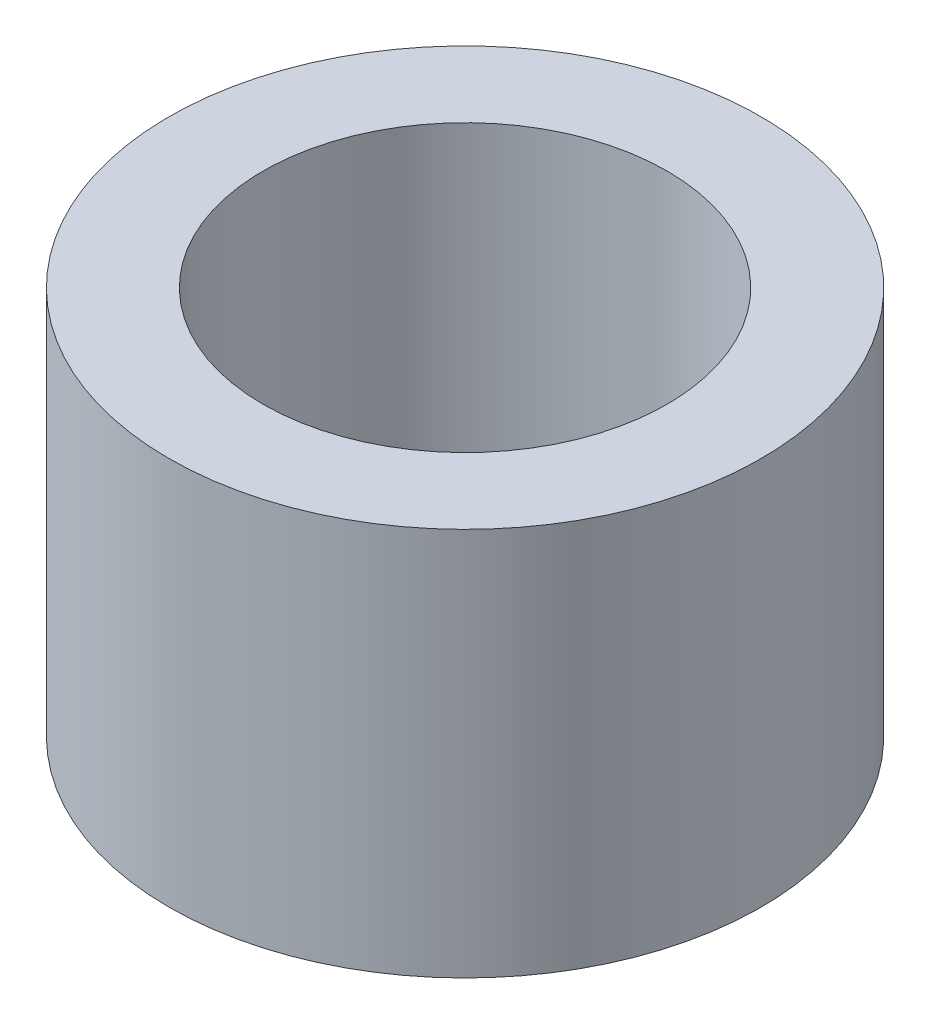
SolidWorks part; units mm, degrees
ref_plane "Front Plane" through (0, 0, 0) normal (0, 0, 1) x (1, 0, 0)
ref_plane "Top Plane" through (0, 0, 0) normal (0, 1, 0) x (1, 0, 0)
ref_plane "Right Plane" through (0, 0, 0) normal (1, 0, 0) x (0, 0, -1)
sketch "Sketch1" plane through (0, 0, 0) normal (0, 1, 0) x (1, 0, 0)
  circle A0 centre (0, 0) radius 2.6
  circle A1 centre (0, 0) radius 3.81
  dimension "D1" = 5.2
  dimension "D2" = 7.62
extrude "Boss-Extrude1" add sketch "Sketch1" along normal blind 5
